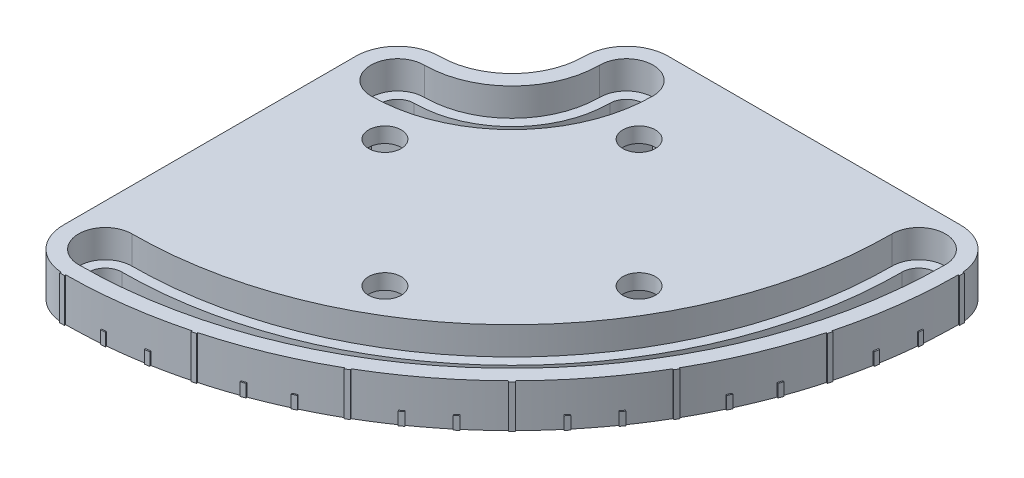
SolidWorks part; units mm, degrees
ref_plane "정면" through (0, 0, 0) normal (0, 0, 1) x (1, 0, 0)
ref_plane "윗면" through (0, 0, 0) normal (0, 1, 0) x (1, 0, 0)
ref_plane "우측면" through (0, 0, 0) normal (1, 0, 0) x (0, 0, -1)
sketch "스케치1" plane through (0, 0, 0) normal (0, 1, 0) x (1, 0, 0)
  line L1 (-8.25, -80) -> (-8.25, -22.5)
  line L7 (22.5, 8.25) -> (80, 8.25)
  arc A0 (0, -19.25) -> (0, -25.75) centre (0, -22.5) ccw
  arc A1 (25.75, 0) -> (19.25, 0) centre (22.5, 0) ccw
  arc A2 (0, -76.75) -> (0, -83.25) centre (0, -80) ccw
  arc A3 (83.25, 0) -> (76.75, 0) centre (80, 0) ccw
  arc A4 (0, -25.75) -> (25.75, 0) centre (0, 0) ccw
  arc A5 (0, -19.25) -> (19.25, 0) centre (0, 0) ccw
  arc A6 (0, -76.75) -> (76.75, 0) centre (0, 0) ccw
  arc A7 (0, -83.25) -> (83.25, 0) centre (0, 0) ccw
  circle A8 centre (58.75, -33.75) radius 3.2
  circle A9 centre (33.75, -58.75) radius 3.2
  circle A10 centre (8.75, -33.75) radius 3.2
  circle A11 centre (33.75, -8.75) radius 3.2
  arc A12 (0, -88.25) -> (88.25, 0) centre (0, 0) ccw
  arc A13 (0, -14.25) -> (14.25, 0) centre (0, 0) ccw
  arc A15 (-8.25, -80) -> (0, -88.25) centre (0, -80) ccw
  arc A16 (88.25, 0) -> (80, 8.25) centre (80, 0) ccw
  arc A17 (0, -14.25) -> (-8.25, -22.5) centre (0, -22.5) ccw
  arc A18 (22.5, 8.25) -> (14.25, 0) centre (22.5, 0) ccw
  point P0 (33.75, -33.75)
  dimension "D7" = 25
  dimension "D10" = 6.4
  dimension "D3" = 6.5
  dimension "D6" = 25
  dimension "D14" = 5
  dimension "D1" = 33.75
  dimension "D2" = 33.75
  dimension "D4" = 22.5
  dimension "D5" = 80
  dimension "D8" = 25
  dimension "D9" = 25
extrude "보스-돌출1" add sketch "스케치1" along normal blind 8.5
sketch "스케치2" plane through (0, 8.5, 0) normal (0, 1, 0) x (1, 0, 0)
  line L0 (0, 0) -> (-0.4634, -88.4988) construction
  line L1 (0, 0) -> (0.4634, -88.4988) construction
  line L2 (0, 0) -> (0, -88.5) construction
  line L3 (0.4581, -87.4988) -> (0.4634, -88.4988)
  line L4 (-0.4581, -87.4988) -> (-0.4634, -88.4988)
  arc A0 (-0.4634, -88.4988) -> (0.4634, -88.4988) centre (0, 0) ccw
  arc A1 (-0.4581, -87.4988) -> (0.4581, -87.4988) centre (0, 0) ccw
  dimension "D3" = 175
  dimension "D4" = 88.5
  dimension "D1" = 0.3
  dimension "D2" = 0.3
extrude "보스-돌출2" add sketch "스케치2" against normal up to surface (8.5 mm away) up to face at (12.7675, 0, 12.7675)
pattern_circular "원형 패턴1" count 7 over 90 about axis through (0, 0, 0) along (0, 1, 0) of "보스-돌출2"
sketch "스케치6" plane through (0, 0, 0) normal (0, -1, 0) x (1, 0, 0)
  line L2 (0, 0) -> (88.25, 0) construction
  line L3 (0, 0) -> (88.2488, 0.4621) construction
  line L6 (0, 0) -> (88.2371, -0.462) construction
  line L7 (88.4988, 0.4634) -> (87.9988, 0.4608)
  line L8 (88.4988, -0.4634) -> (87.9988, -0.4608)
  arc A1 (87.9988, -0.4608) -> (87.9988, 0.4608) centre (0, 0) ccw
  arc A2 (88.4988, -0.4634) -> (88.4988, 0.4634) centre (0, 0) ccw
  arc A4 (88.2488, 0.4621) -> (85.3614, 22.3941) centre (0, 0) ccw construction
  arc A5 (80, -8.25) -> (88.2371, -0.462) centre (80, 0) ccw construction
  dimension "D1" = 176
  dimension "D2" = 0.3
  dimension "D4" = 88.5
  dimension "D3" = 0.3
extrude "보스-돌출3" add sketch "스케치6" against normal blind 2.5
pattern_circular "원형 패턴2" count 19 over 90 about axis through (0, 8.5, 0) along (0, -1, 0) of "보스-돌출3"
sketch "스케치7" plane through (0, 0, 0) normal (0, -1, 0) x (1, 0, 0)
  line L0 (0, 0) -> (8.75, 33.75) construction
  line L1 (0, 0) -> (33.75, 58.75) construction
  line L2 (58.75, 33.75) -> (0, 0) construction
  line L3 (0, 0) -> (33.75, 8.75) construction
  line L4 (26.6508, 56.8313) -> (35.6687, 51.6508)
  line L5 (26.6508, 56.8313) -> (31.8313, 65.8492)
  line L6 (35.6687, 51.6508) -> (40.8492, 60.6687)
  line L7 (31.8313, 65.8492) -> (40.8492, 60.6687)
  line L8 (26.6508, 56.8313) -> (40.8492, 60.6687) construction
  line L9 (35.6687, 51.6508) -> (31.8313, 65.8492) construction
  line L10 (51.6508, 35.6687) -> (56.8313, 26.6508)
  line L11 (51.6508, 35.6687) -> (60.6687, 40.8492)
  line L12 (56.8313, 26.6508) -> (65.8492, 31.8313)
  line L13 (60.6687, 40.8492) -> (65.8492, 31.8313)
  line L14 (51.6508, 35.6687) -> (65.8492, 31.8313) construction
  line L15 (56.8313, 26.6508) -> (60.6687, 40.8492) construction
  line L16 (30.0214, 2.4114) -> (40.0886, 5.0214)
  line L17 (30.0214, 2.4114) -> (27.4114, 12.4786)
  line L18 (40.0886, 5.0214) -> (37.4786, 15.0886)
  line L19 (27.4114, 12.4786) -> (37.4786, 15.0886)
  line L20 (30.0214, 2.4114) -> (37.4786, 15.0886) construction
  line L21 (40.0886, 5.0214) -> (27.4114, 12.4786) construction
  line L22 (2.4114, 30.0214) -> (12.4786, 27.4114)
  line L23 (2.4114, 30.0214) -> (5.0214, 40.0886)
  line L24 (12.4786, 27.4114) -> (15.0886, 37.4786)
  line L25 (5.0214, 40.0886) -> (15.0886, 37.4786)
  line L26 (2.4114, 30.0214) -> (15.0886, 37.4786) construction
  line L27 (12.4786, 27.4114) -> (5.0214, 40.0886) construction
  point P5 (33.75, 58.75)
  point P6 (58.75, 33.75)
  point P7 (33.75, 8.75)
  point P12 (8.75, 33.75)
  dimension "D1" = 10.4
extrude "컷-돌출1" cut sketch "스케치7" against normal offset from surface (5.5 mm away) 3 up to face at (47.6951, 8.5, 47.6951)
sketch "스케치8" plane through (0, 8.5, 0) normal (0, 1, 0) x (1, 0, 0)
  arc A0 (27.75, 0) -> (17.25, 0) centre (22.5, 0) ccw
  arc A1 (85.25, 0) -> (74.75, 0) centre (80, 0) ccw
  arc A2 (0, -17.25) -> (0, -27.75) centre (0, -22.5) ccw
  arc A3 (0, -74.75) -> (0, -85.25) centre (0, -80) ccw
  arc A4 (0, -17.25) -> (17.25, 0) centre (0, 0) ccw
  arc A5 (0, -27.75) -> (27.75, 0) centre (0, 0) ccw
  arc A6 (0, -74.75) -> (74.75, 0) centre (0, 0) ccw
  arc A7 (0, -85.25) -> (85.25, 0) centre (0, 0) ccw
  dimension "D1" = 10.5
extrude "컷-돌출2" cut sketch "스케치8" against normal offset from surface (5.5 mm away) 3 up to face at (58.75, 0, 33.75)
